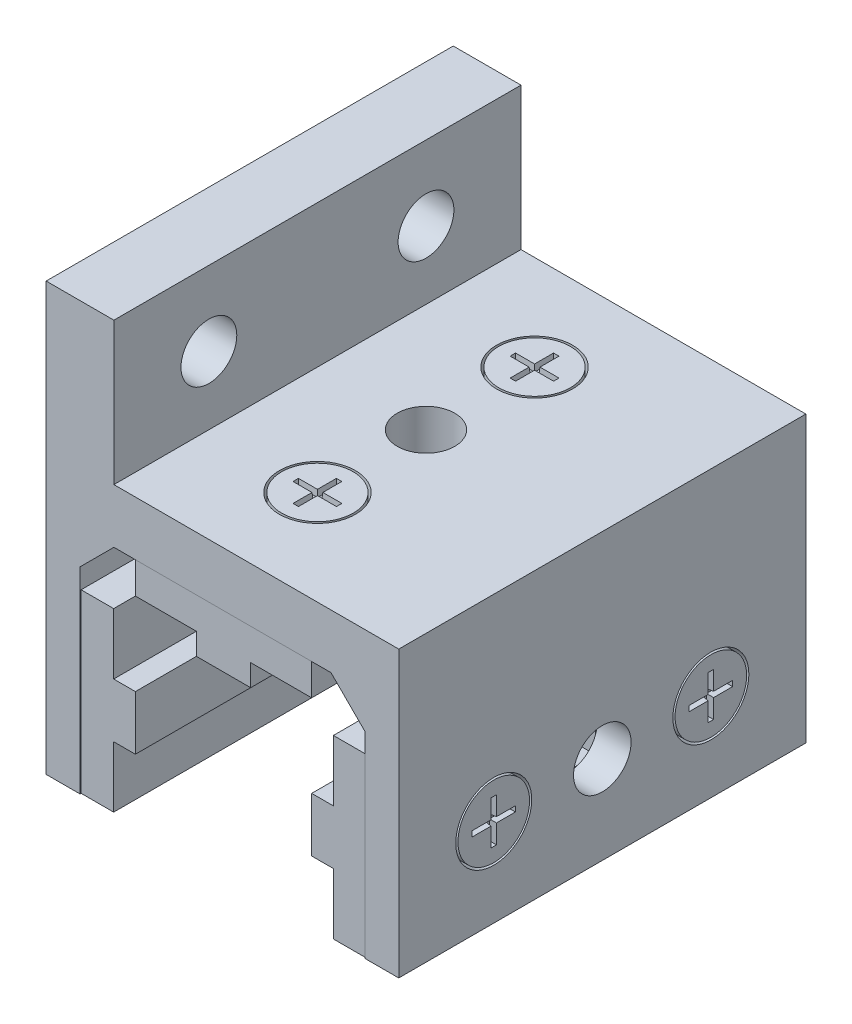
SolidWorks part; units mm, degrees
ref_plane "Front" through (0, 0, 0) normal (0, 0, 1) x (1, 0, 0)
ref_plane "Top" through (0, 0, 0) normal (0, 1, 0) x (1, 0, 0)
ref_plane "Right" through (0, 0, 0) normal (1, 0, 0) x (0, 0, -1)
sketch "Sketch1" plane through (0, 0, 0) normal (0, 0, 1) x (1, 0, 0)
  line L0 (-16.6624, 0) -> (-16.6624, 23.0124)
  line L1 (-20.6248, 33.3248) -> (20.6248, 33.3248)
  line L2 (-20.6248, 33.3248) -> (-20.6248, 0)
  line L3 (-20.6248, 0) -> (-16.6624, 0)
  line L4 (20.6248, 33.3248) -> (20.6248, 0)
  line L5 (-16.6624, 23.0124) -> (-12.7, 26.9748)
  line L6 (-12.7, 26.9748) -> (12.7, 26.9748)
  line L7 (12.7, 26.9748) -> (16.6624, 23.0124)
  line L8 (16.6624, 23.0124) -> (16.6624, 0)
  line L9 (16.6624, 0) -> (20.6248, 0)
  line L11 (-16.6624, 0) -> (16.6624, 0) construction
  dimension "D2" = 45
extrude "Boss-Extrude1" add sketch "Sketch1" along normal mid plane 47.625
sketch "Sketch2" plane through (0, 0, 0) normal (0, 0, 1) x (1, 0, 0)
  line L0 (-12.8524, 13.4874) -> (-12.8524, 20.6248)
  line L1 (-16.6624, 0) -> (-12.8524, 0)
  line L2 (-16.6624, 0) -> (-16.6624, 20.6248)
  line L3 (-16.6624, 20.6248) -> (-12.8524, 20.6248)
  line L4 (-12.8524, 0) -> (-12.8524, 7.1374)
  line L5 (-12.8524, 13.4874) -> (-10.3124, 13.4874)
  line L7 (-12.8524, 7.1374) -> (-10.3124, 7.1374)
  line L8 (-10.3124, 13.4874) -> (-10.3124, 7.1374)
  line L12 (-12.7, 26.9748) -> (12.7, 26.9748) construction
  line L13 (-10.3124, 26.9748) -> (10.3124, 26.9748)
  line L14 (-10.3124, 26.9748) -> (-10.3124, 23.1648)
  line L15 (-10.3124, 23.1648) -> (-3.175, 23.1648)
  line L16 (10.3124, 26.9748) -> (10.3124, 23.1648)
  line L17 (3.175, 23.1648) -> (10.3124, 23.1648)
  line L19 (-3.175, 23.1648) -> (-3.175, 20.6248)
  line L20 (-3.175, 20.6248) -> (3.175, 20.6248)
  line L21 (3.175, 23.1648) -> (3.175, 20.6248)
  point P14 (-10.3124, 10.3124)
  point P28 (0, 26.9748)
  dimension "Pad Wd" = 20.6248
  dimension "Pad Thick 1" = 6.35
  dimension "Pad Thick 2" = 3.81
  dimension "Pad Nose" = 6.35
extrude "Boss-Extrude2" add sketch "Sketch2" along normal mid plane 47.371 separate body
sketch "Sketch11" plane through (-10.3124, 0, 0) normal (1, 0, 0) x (0, 0, -1)
  line L0 (-23.6855, 13.4874) -> (23.6855, 13.4874) construction
  line L1 (-3.175, 13.4874) -> (3.175, 13.4874)
  line L2 (-3.175, 13.4874) -> (-3.175, 7.1374)
  line L3 (-3.175, 7.1374) -> (3.175, 7.1374)
  line L4 (3.175, 13.4874) -> (3.175, 7.1374)
  line L5 (-23.6855, 7.1374) -> (23.6855, 7.1374) construction
  point P8 (0, 13.4874)
extrude "Cut-Extrude5" cut sketch "Sketch11" against normal through all
sketch "Sketch12" plane through (0, 20.6248, 0) normal (0, -1, 0) x (1, 0, 0)
  line L0 (-3.175, 23.6855) -> (-3.175, -23.6855) construction
  line L1 (-3.175, 3.175) -> (3.175, 3.175)
  line L2 (-3.175, 3.175) -> (-3.175, -3.175)
  line L3 (-3.175, -3.175) -> (3.175, -3.175)
  line L4 (3.175, 3.175) -> (3.175, -3.175)
  line L5 (3.175, 23.6855) -> (3.175, -23.6855) construction
  point P8 (-3.175, 0)
extrude "Cut-Extrude6" cut sketch "Sketch12" against normal through all
mirror "Mirror1" about plane through (0, 0, 0) normal (1, 0, 0) of bodies 126 109
sketch "Sketch3" plane through (0, 33.3248, 0) normal (0, 1, 0) x (1, 0, 0)
  line L0 (0, -12.7) -> (0, 12.7) construction
  circle A0 centre (0, -12.7) radius 4.445
  circle A1 centre (0, -12.7) radius 4.191
extrude "Cut-Extrude1" cut sketch "Sketch3" against normal blind 3.175
sketch "Sketch5" plane through (0, 33.3248, 0) normal (0, 1, 0) x (1, 0, 0)
  line L0 (0.3175, -12.3825) -> (2.54, -12.3825)
  line L1 (-0.3175, -10.16) -> (0.3175, -10.16)
  line L2 (-0.3175, -10.16) -> (-0.3175, -12.3825)
  line L3 (-0.3175, -15.24) -> (0.3175, -15.24)
  line L4 (0.3175, -10.16) -> (0.3175, -12.3825)
  line L5 (-2.54, -12.3825) -> (-0.3175, -12.3825)
  line L6 (-2.54, -12.3825) -> (-2.54, -13.0175)
  line L7 (-2.54, -13.0175) -> (-0.3175, -13.0175)
  line L8 (2.54, -12.3825) -> (2.54, -13.0175)
  line L9 (-0.3175, -13.0175) -> (-0.3175, -15.24)
  line L10 (0.3175, -13.0175) -> (0.3175, -15.24)
  line L11 (0.3175, -13.0175) -> (2.54, -13.0175)
  line L12 (-0.3175, -12.3825) -> (0.3175, -13.0175) construction
  dimension "D1" = 0.635
  dimension "D2" = 5.08
extrude "Cut-Extrude2" cut sketch "Sketch5" against normal blind 0.762 draft 5
sketch "Sketch13" plane through (20.6248, 0, 0) normal (1, 0, 0) x (0, 0, -1)
  circle A0 centre (-12.7, 10.3124) radius 4.445
  dimension "D1" = 8.89
extrude "Cut-Extrude-Thin1" cut sketch "Sketch13" against normal blind 1.9812 thin thin type one direction reverse wall 0.254
sketch "Sketch14" plane through (20.6248, 0, 0) normal (1, 0, 0) x (0, 0, -1)
  line L0 (-13.0175, 9.9949) -> (-13.0175, 7.7724)
  line L1 (-13.0175, 12.8524) -> (-12.3825, 12.8524)
  line L2 (-13.0175, 12.8524) -> (-13.0175, 10.6299)
  line L3 (-13.0175, 7.7724) -> (-12.3825, 7.7724)
  line L4 (-12.3825, 12.8524) -> (-12.3825, 10.6299)
  line L5 (-15.24, 10.6299) -> (-13.0175, 10.6299)
  line L6 (-15.24, 10.6299) -> (-15.24, 9.9949)
  line L7 (-15.24, 9.9949) -> (-13.0175, 9.9949)
  line L8 (-10.16, 10.6299) -> (-10.16, 9.9949)
  line L9 (-12.3825, 10.6299) -> (-10.16, 10.6299)
  line L10 (-12.3825, 9.9949) -> (-12.3825, 7.7724)
  line L11 (-12.3825, 9.9949) -> (-10.16, 9.9949)
  line L12 (-13.0175, 10.6299) -> (-12.3825, 9.9949) construction
  dimension "D1" = 0.635
  dimension "D2" = 5.08
extrude "Cut-Extrude7" cut sketch "Sketch14" against normal blind 0.762 draft 5
mirror "Mirror4" about plane through (0, 0, 0) normal (1, 0, 0) of "Cut-Extrude7", "Cut-Extrude-Thin1"
mirror "Mirror3" about plane through (0, 0, 0) normal (0, 0, 1) of "Mirror4", "Cut-Extrude-Thin1", "Cut-Extrude7", "Cut-Extrude1", "Cut-Extrude2"
sketch "Sketch9" plane through (0, 33.3248, 0) normal (0, 1, 0) x (1, 0, 0)
  circle A0 centre (0, 0) radius 3.3655
  dimension "Top Hole Dia" = 6.731
extrude "Cut-Extrude4" cut sketch "Sketch9" against normal through all
sketch "Sketch15" plane through (0, 0, 0) normal (1, 0, 0) x (0, 0, -1)
  circle A0 centre (0, 10.3124) radius 3.3655
  dimension "Side Wall Hole Dia" = 6.731
extrude "Cut-Extrude8" cut sketch "Sketch15" against normal through all and the other way through all
sketch "Sketch6" plane through (0, 0, 0) normal (0, 0, 1) x (1, 0, 0)
  line L0 (-20.6248, 0) -> (-16.6624, 0) construction
  line L1 (-20.6248, 26.9748) -> (-12.7, 26.9748)
  line L2 (-20.6248, 26.9748) -> (-20.6248, 49.9872)
  line L3 (-20.6248, 49.9872) -> (-12.7, 49.9872)
  line L4 (-12.7, 26.9748) -> (-12.7, 49.9872)
  line L5 (-12.7, 26.9748) -> (12.7, 26.9748) construction
  line L6 (-20.6248, 33.3248) -> (-20.6248, 0) construction
  dimension "Oall Ht" = 49.9872
  dimension "Side Flange Thickness" = 7.9248
extrude "Side Flange" add sketch "Sketch6" along normal up to surface and the other way up to surface
sketch "Sketch7" plane through (0, 0, 0) normal (1, 0, 0) x (0, 0, -1)
  line L0 (-12.7, 41.275) -> (12.7, 41.275) construction
  line L2 (-23.8125, 0) -> (23.8125, 0) construction
  line L3 (-12.7, 30.1498) -> (-12.7, 33.3248) construction
  circle A0 centre (-12.7, 41.275) radius 3.2639
  circle A1 centre (12.7, 41.275) radius 3.2639
  point P4 (0, 41.275)
  dimension "Side Flange Hole Dia" = 6.5278
  dimension "Side Flange Hole Spacing" = 41.275
extrude "Side Flange Hole" cut sketch "Sketch7" against normal through all
sketch "Sketch16" plane through (0, 0, 0) normal (0, 0, 1) x (1, 0, 0)
  line L1 (-20.6248, 33.3248) -> (-18.6436, 33.3248)
  line L2 (-20.6248, 33.3248) -> (-20.6248, 25.4)
  line L3 (-20.6248, 25.4) -> (-18.6436, 25.4)
  line L4 (-18.6436, 33.3248) -> (-18.6436, 25.4)
  line L5 (20.6248, 33.3248) -> (-12.7, 33.3248) construction
  line L6 (18.6436, 33.3248) -> (20.6248, 33.3248)
  line L7 (18.6436, 33.3248) -> (18.6436, 25.4)
  line L8 (18.6436, 25.4) -> (20.6248, 25.4)
  line L9 (20.6248, 33.3248) -> (20.6248, 25.4)
  line L10 (-20.6248, 0) -> (-16.6624, 0) construction
  line L11 (16.6624, 0) -> (20.6248, 0) construction
  point P4 (-18.6436, 0)
  point P13 (18.6436, 0)
  dimension "Oall Wd" = 41.2496
  dimension "Top Flange Thickness" = 7.9248
extrude "Top Flange" add sketch "Sketch16" along normal up to surface (23.8125 mm away) and the other way up to surface (23.8125 mm away) up to face at (-2.1167, 22.2165, 23.8125) other way up to face at (-2.1167, 22.2165, -23.8125)
equation "\"D1@Cut-Extrude1\" = \"Top Thick@Sketch1\" * .5"
equation "\"D1@Sketch13\" = \"Screw Head Dia@Sketch3\""
equation "\"D1@Cut-Extrude-Thin1\" = \"Leg Thick@Sketch1\" * .5"
equation "\"D5@Cut-Extrude-Thin1\" = \"D1@Sketch3\""
equation "\"D1@Cut-Extrude7\" = \"D1@Cut-Extrude2\""
equation "\"D1@Sketch14\" = \"D1@Sketch5\""
equation "\"D2@Sketch14\" = \"D2@Sketch5\""
equation "\"D3@Cut-Extrude7\" = \"D3@Cut-Extrude2\""
